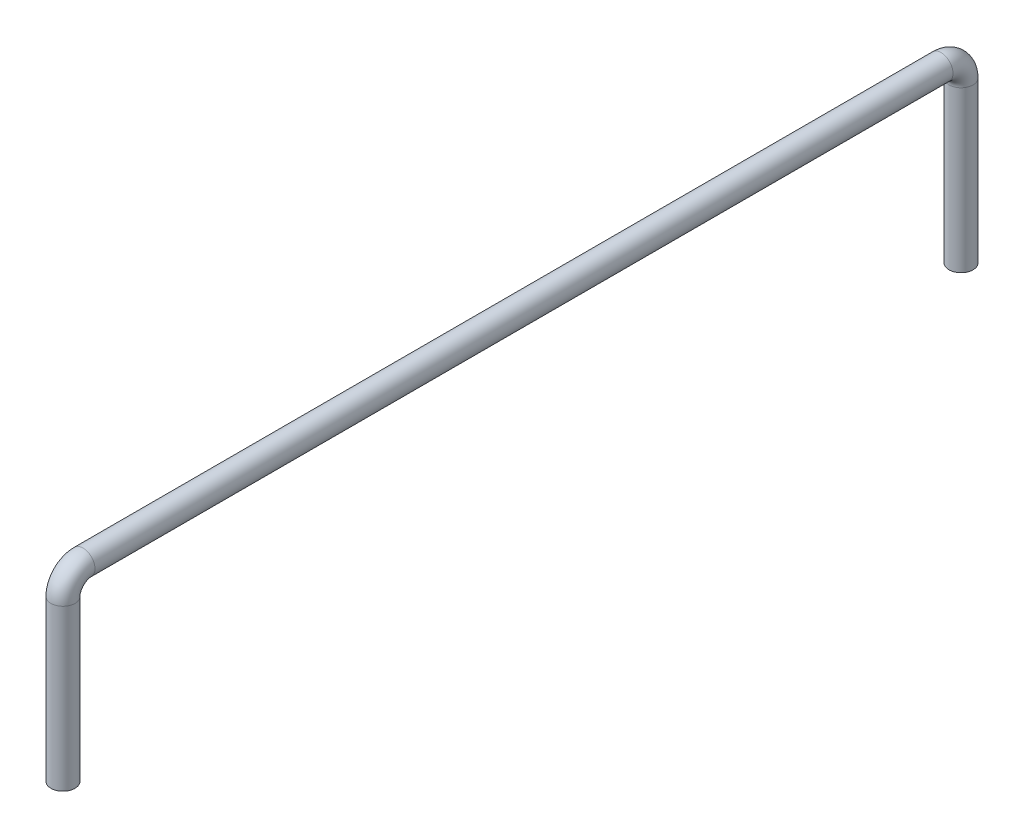
SolidWorks part; units mm, degrees
material "AISI 1045 Steel, cold drawn"
ref_plane "Front Plane" through (0, 0, 0) normal (0, 0, 1) x (1, 0, 0)
ref_plane "Top Plane" through (0, 0, 0) normal (0, 1, 0) x (1, 0, 0)
ref_plane "Right Plane" through (0, 0, 0) normal (1, 0, 0) x (0, 0, -1)
sketch "Sketch1" plane through (0, 0, 0) normal (0, 1, 0) x (1, 0, 0)
  circle A0 centre (0, 0) radius 0.5
  circle A1 centre (0, -44.1855) radius 0.6
  dimension "D1" = 1
  dimension "D2" = 1.2
  dimension "D3" = 44.1855
sketch "Sketch4" plane through (0, 0, 0) normal (1, 0, 0) x (0, 0, -1)
  line L0 (-43.8592, 9) -> (-1, 9)
  line L2 (0, 0) -> (0, 8)
  line L3 (-44.8592, 8) -> (-44.8592, 0)
  arc A0 (0, 8) -> (-1, 9) centre (-1, 8) ccw
  arc A1 (-43.8592, 9) -> (-44.8592, 8) centre (-43.8592, 8) ccw
  dimension "D3" = 1
  dimension "D4" = 2
  dimension "D1" = 42.8592
  dimension "D2" = 8
  dimension "D5" = 1
  dimension "D6" = 1
sweep "Sweep4" add path "Sketch4" circular profile diameter 1.2 parameters "D3"=1.2
